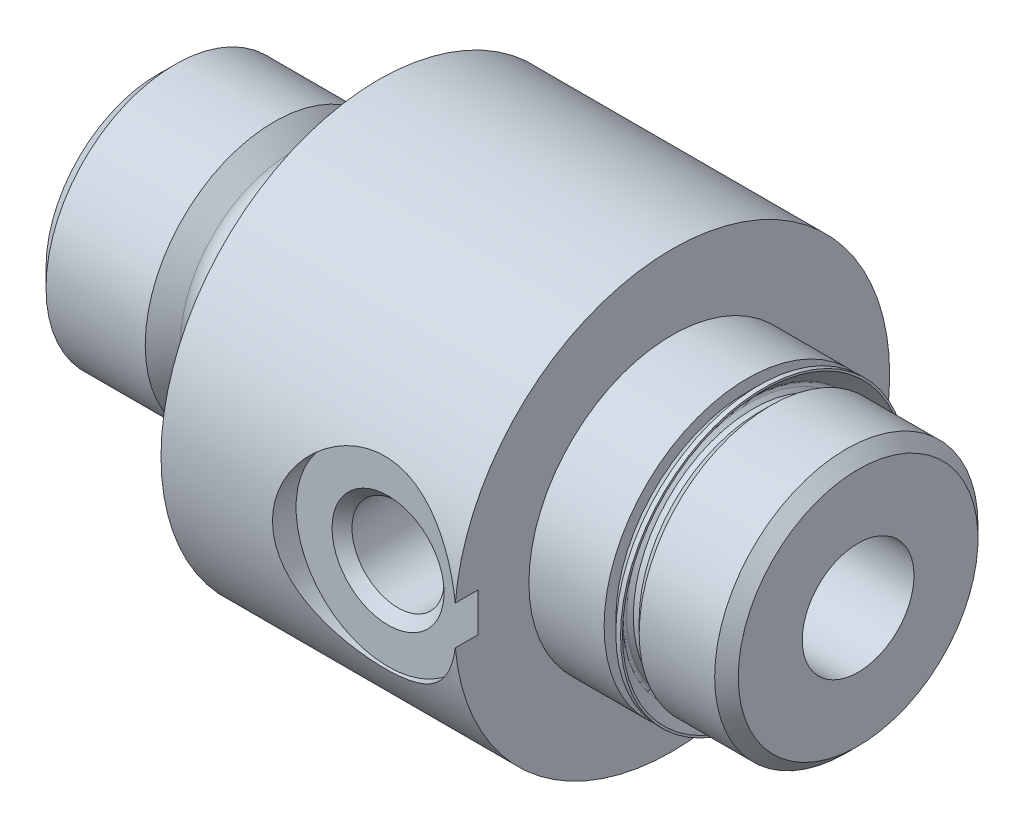
SolidWorks part; units mm, degrees
ref_plane "Front Plane" through (0, 0, 0) normal (0, 0, 1) x (1, 0, 0)
ref_plane "Top Plane" through (0, 0, 0) normal (0, 1, 0) x (1, 0, 0)
ref_plane "Right Plane" through (0, 0, 0) normal (1, 0, 0) x (0, 0, -1)
ref_plane "Plane1" through (0, 0, 0) normal (0, 0, 1) x (1, 0, 0)
sketch "Sketch1" plane through (0, 0, 0) normal (0, 0, 1) x (1, 0, 0)
  line L0 (0, 0) -> (0, 4.8006)
  line L1 (0, 4.8006) -> (0.7556, 5.5563)
  line L2 (0.7556, 5.5563) -> (5.0286, 5.5563)
  line L3 (5.0286, 5.5563) -> (5.7864, 4.8042)
  line L4 (6.35, 4.572) -> (7.5184, 4.572)
  line L5 (8.3185, 5.3721) -> (8.3185, 5.5245)
  line L6 (8.3185, 5.5245) -> (9.525, 5.5245)
  line L7 (9.525, 5.5245) -> (9.525, 0)
  line L8 (9.525, 0) -> (0, 0)
  line L9 (9.525, 0) -> (0, 0) construction
  arc A0 (5.7864, 4.8042) -> (6.35, 4.572) centre (6.35, 5.3721) ccw
  arc A1 (7.5184, 4.572) -> (8.3185, 5.3721) centre (7.5184, 5.3721) ccw
revolve "Revolve1" add sketch "Sketch1" angle 360 about L9
cosmetic thread "Cosmetic Thread1" parameters "D1"=5.7842, "D2"=9.6012
ref_plane "Plane2" through (0, 0, 0) normal (0, 0, 1) x (1, 0, 0)
sketch "Sketch2" plane through (0, 0, 0) normal (0, 0, 1) x (1, 0, 0)
  line L0 (9.525, 0) -> (9.525, 9.3726)
  line L1 (9.525, 9.3726) -> (25.4, 9.3726)
  line L2 (25.4, 9.3726) -> (25.4, 5.1626)
  line L3 (25.4, 5.1626) -> (25.908, 5.1626)
  line L4 (25.908, 5.1626) -> (26.416, 5.6705)
  line L5 (26.416, 5.6705) -> (29.6672, 5.6705)
  line L6 (29.6672, 5.6705) -> (30.1752, 5.1626)
  line L7 (30.1752, 5.1626) -> (30.1752, 0)
  line L8 (30.1752, 0) -> (9.525, 0)
  line L9 (30.1752, 0) -> (9.525, 0) construction
revolve "Revolve2" add sketch "Sketch2" angle 360 about L9
ref_plane "Plane3" through (0, 0, 0) normal (0, 0, 1) x (1, 0, 0)
sketch "Sketch3" plane through (0, 0, 0) normal (0, 0, 1) x (1, 0, 0)
  line L0 (0, 0) -> (0, 2.9146)
  line L1 (0, 2.9146) -> (0.508, 2.4067)
  line L2 (0.508, 2.4067) -> (30.1752, 2.4067)
  line L3 (30.1752, 2.4067) -> (30.1752, 0)
  line L4 (30.1752, 0) -> (0, 0)
  line L5 (30.1752, 0) -> (0, 0) construction
revolve "Cut-Revolve1" cut sketch "Sketch3" angle 360 about L5
ref_plane "Plane4" through (0, 0, 0) normal (0, 1, 0) x (1, 0, 0)
sketch "Sketch4" plane through (0, 0, 0) normal (0, 1, 0) x (1, 0, 0)
  line L0 (18.288, 1.016) -> (20.2717, 1.016)
  line L1 (20.2717, 1.016) -> (20.2717, -7.9273)
  line L2 (20.2717, -7.9273) -> (20.701, -8.3566)
  line L3 (20.701, -8.3566) -> (22.2504, -8.3566)
  line L4 (22.2504, -8.3566) -> (22.2504, -9.3726)
  line L5 (22.2504, -9.3726) -> (18.288, -9.3726)
  line L6 (18.288, -9.3726) -> (18.288, 1.016)
  line L7 (18.288, -9.3726) -> (18.288, 1.016) construction
revolve "Cut-Revolve2" cut sketch "Sketch4" angle 360 about L7
ref_plane "Plane5" through (0, 0, 0) normal (0, 0, 1) x (1, 0, 0)
sketch "Sketch5" plane through (0, 0, 0) normal (0, 0, 1) x (1, 0, 0)
  line L0 (22.1615, 9.9758) -> (22.1615, 6.1658)
  line L1 (22.1615, 6.1658) -> (25.4, 6.1658)
  line L2 (25.4, 6.1658) -> (25.4, 9.9758)
  line L3 (25.4, 9.9758) -> (22.1615, 9.9758)
  line L4 (25.4, 0) -> (22.1615, 0) construction
revolve "Cut-Revolve3" cut sketch "Sketch5" angle 360 about L4
ref_plane "Plane6" through (0, 0, 0) normal (0, 0, 1) x (1, 0, 0)
sketch "Sketch6" plane through (0, 0, 0) normal (0, 0, 1) x (1, 0, 0)
  line L0 (25.4, 5.6603) -> (25.4, 4.9085)
  line L1 (25.4, 4.9085) -> (25.908, 4.9085)
  line L2 (25.908, 4.9085) -> (25.908, 5.1626)
  line L3 (25.908, 5.1626) -> (25.654, 5.1626)
  line L4 (25.654, 5.1626) -> (25.5116, 5.305)
  line L5 (25.5116, 5.4846) -> (26.1087, 6.0817)
  line L6 (26.1087, 6.0817) -> (26.1087, 6.1658)
  line L7 (26.1087, 6.1658) -> (25.9055, 6.1658)
  line L8 (25.9055, 6.1658) -> (25.4, 5.6603)
  line L9 (25.908, 0) -> (25.4, 0) construction
  arc A0 (25.5116, 5.305) -> (25.5116, 5.4846) centre (25.6014, 5.3948) cw
revolve "Revolve3" add sketch "Sketch6" angle 360 about L9
